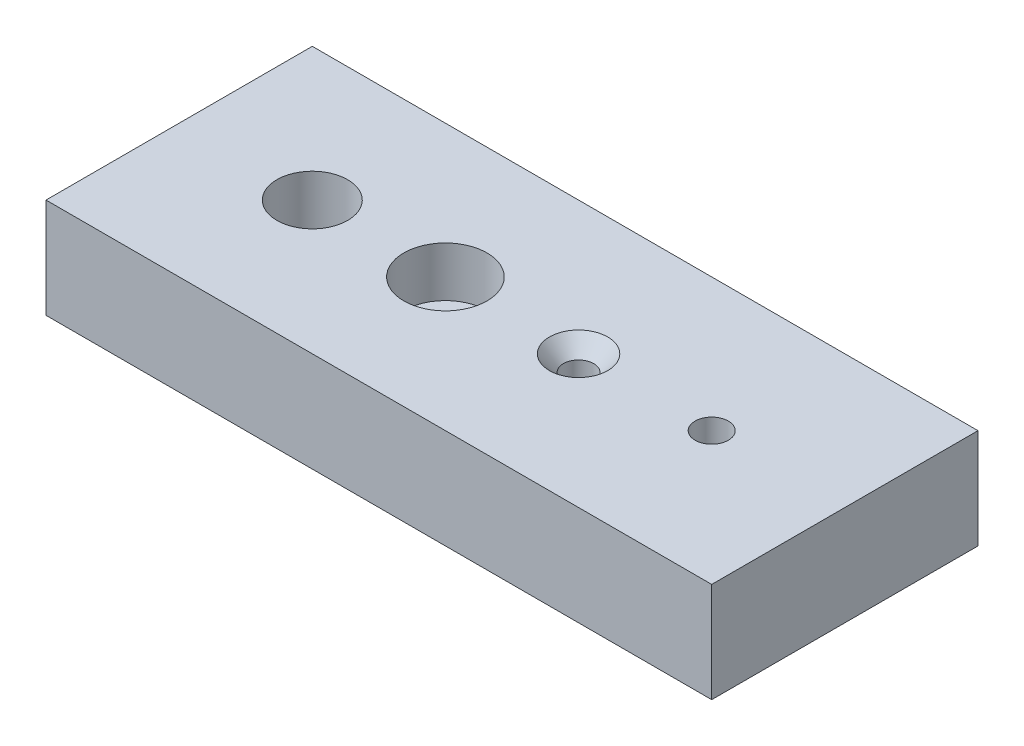
SolidWorks part; units mm, degrees
ref_plane "Front Plane" through (0, 0, 0) normal (0, 0, 1) x (1, 0, 0)
ref_plane "Top Plane" through (0, 0, 0) normal (0, 1, 0) x (1, 0, 0)
ref_plane "Right Plane" through (0, 0, 0) normal (1, 0, 0) x (0, 0, -1)
sketch "Sketch1" plane through (0, 0, 0) normal (0, 0, 1) x (1, 0, 0)
  line L1 (0, 0) -> (127, 0)
  line L2 (0, 0) -> (0, 19.05)
  line L3 (0, 19.05) -> (127, 19.05)
  line L4 (127, 0) -> (127, 19.05)
  dimension "D1" = 19.05
  dimension "D2" = 127
extrude "Boss-Extrude1" add sketch "Sketch1" along normal blind 50.8
hole_wizard "1/2 Clearance Hole1" positions "Sketch2" profile "Sketch3" hole size "1/2" standard "ANSI Inch" end condition through all
sketch "Sketch2" plane through (0, 19.05, 0) normal (0, 1, 0) x (1, 0, 0)
  line L0 (0, -50.8) -> (0, 0) construction
  line L1 (127, -50.8) -> (0, -50.8) construction
  point P0 (25.4, -25.4)
  dimension "D1" = 25.4
  dimension "D2" = 25.4
sketch "Sketch3" plane through (25.4, 19.05, 25.4) normal (1, 0, 0) x (0, 0, 1)
  line L0 (0, 0) -> (0, 19.05)
  line L1 (0, 19.05) -> (6.7462, 19.05)
  line L2 (6.7462, 19.05) -> (6.7462, 0)
  line L5 (6.7462, 0) -> (0, 0)
  line L11 (0, -6.35) -> (0, 107.95) construction
  dimension "Thru Hole Dia." = 13.4925
  dimension "Thru Hole Depth" = 19.05
hole_wizard "CBORE for 3/8 Socket Head Cap Screw1" positions "Sketch4" profile "Sketch5" counterbore size "3/8" standard "ANSI Inch" end condition through all
sketch "Sketch4" plane through (0, 19.05, 0) normal (0, 1, 0) x (1, 0, 0)
  line L0 (0, -50.8) -> (0, 0) construction
  line L1 (127, -50.8) -> (0, -50.8) construction
  point P0 (50.8, -25.4)
  dimension "D1" = 50.8
  dimension "D2" = 25.4
sketch "Sketch5" plane through (50.8, 19.05, 25.4) normal (1, 0, 0) x (0, 0, 1)
  line L0 (0, 0) -> (0, 19.05)
  line L1 (0, 19.05) -> (4.9022, 19.05)
  line L3 (4.9022, 19.05) -> (4.9022, 9.525)
  line L4 (4.9022, 9.525) -> (7.9375, 9.525)
  line L5 (7.9375, 9.525) -> (7.9375, 0)
  line L7 (7.9375, 0) -> (0, 0)
  line L11 (0, -6.35) -> (0, 107.95) construction
  dimension "Thru Hole Dia." = 9.8044
  dimension "Thru Hole Depth" = 19.05
  dimension "C'Bore Dia." = 15.875
  dimension "C'Bore Depth" = 9.525
hole_wizard "CSK for #12 Flat Head Machine Screw1" positions "Sketch6" profile "Sketch7" countersink size "#12" standard "ANSI Inch" end condition through all
sketch "Sketch6" plane through (0, 19.05, 0) normal (0, 1, 0) x (1, 0, 0)
  line L0 (0, -50.8) -> (0, 0) construction
  line L1 (127, -50.8) -> (0, -50.8) construction
  point P0 (76.2, -25.4)
  dimension "D1" = 76.2
  dimension "D2" = 25.4
sketch "Sketch7" plane through (76.2, 19.05, 25.4) normal (1, 0, 0) x (0, 0, 1)
  line L0 (0, 0) -> (0, 19.05)
  line L1 (0, 19.05) -> (2.8956, 19.05)
  line L2 (2.8956, 19.05) -> (2.8956, 3.068)
  line L3 (2.8956, 3.068) -> (5.5626, 0)
  line L5 (5.5626, 0) -> (0, 0)
  line L6 (-2.8956, 3.068) -> (-5.5626, 0) construction
  line L11 (0, -6.35) -> (0, 107.95) construction
  dimension "Thru Hole Dia." = 5.7912
  dimension "Thru Hole Depth" = 19.05
  dimension "Near C'Sink Dia." = 11.1252
  dimension "Near C'Sink Angle" = 82
hole_wizard "1/4 (0.2500) Dowel Hole1" positions "Sketch8" profile "Sketch9" hole size "1/4" standard "ANSI Inch" end condition through all
sketch "Sketch8" plane through (0, 19.05, 0) normal (0, 1, 0) x (1, 0, 0)
  line L0 (0, -50.8) -> (0, 0) construction
  line L1 (127, -50.8) -> (0, -50.8) construction
  point P0 (101.6, -25.4)
  dimension "D1" = 101.6
  dimension "D2" = 25.4
sketch "Sketch9" plane through (101.6, 19.05, 25.4) normal (1, 0, 0) x (0, 0, 1)
  line L0 (0, 0) -> (0, 19.05)
  line L1 (0, 19.05) -> (3.175, 19.05)
  line L2 (3.175, 19.05) -> (3.175, 0)
  line L5 (3.175, 0) -> (0, 0)
  line L11 (0, -6.35) -> (0, 107.95) construction
  dimension "Thru Hole Dia." = 6.35
  dimension "Thru Hole Depth" = 19.05
